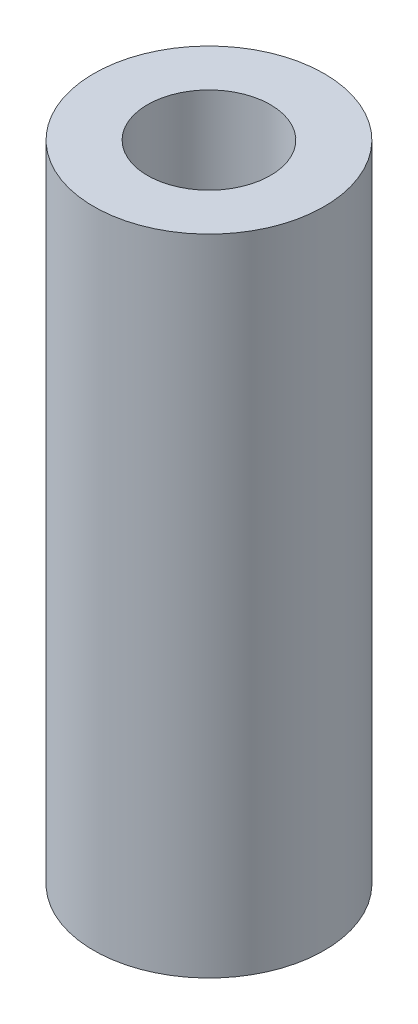
SolidWorks part; units mm, degrees
ref_plane "Спереди" through (0, 0, 0) normal (0, 0, 1) x (1, 0, 0)
ref_plane "Сверху" through (0, 0, 0) normal (0, 1, 0) x (1, 0, 0)
ref_plane "Справа" through (0, 0, 0) normal (1, 0, 0) x (0, 0, -1)
sketch "Эскиз1" plane through (0, 0, 0) normal (0, 0, 1) x (1, 0, 0)
  line L0 (0, 0) -> (-7.5, 0)
  line L1 (-7.5, 0) -> (-7.5, 41.9368)
  line L2 (-7.5, 41.9368) -> (-4, 41.9368)
  line L3 (-4, 41.9368) -> (-4, 18)
  line L4 (-4, 18) -> (0, 18)
  line L5 (0, 18) -> (0, 0)
  line L6 (0, -2.345) -> (0, 38.7846) construction
revolve "Повернуть1" add sketch "Эскиз1" angle 360 about L6
